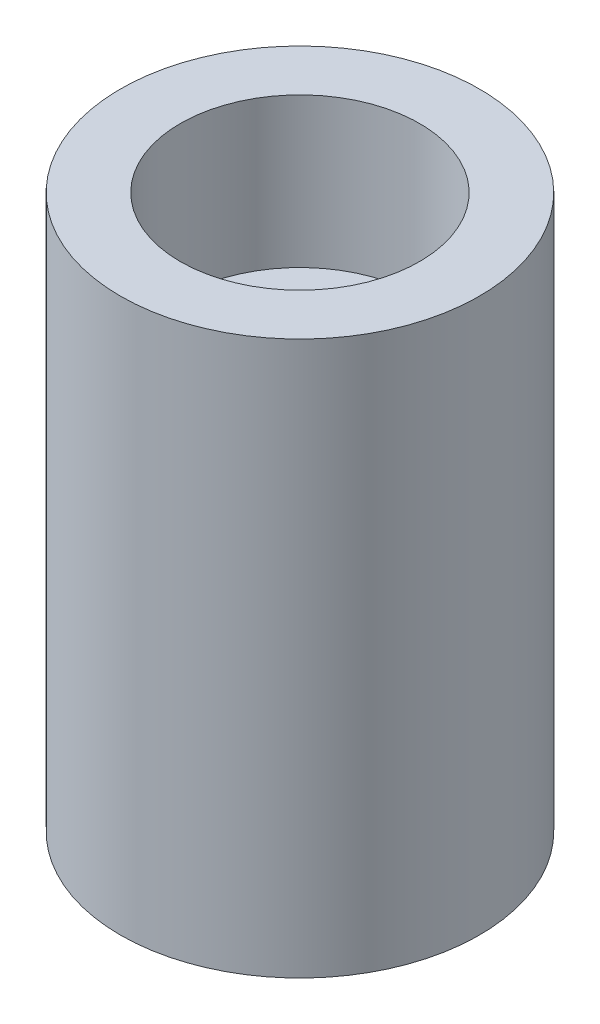
SolidWorks part; units mm, degrees
ref_plane "Front Plane" through (0, 0, 0) normal (0, 0, 1) x (1, 0, 0)
ref_plane "Top Plane" through (0, 0, 0) normal (0, 1, 0) x (1, 0, 0)
ref_plane "Right Plane" through (0, 0, 0) normal (1, 0, 0) x (0, 0, -1)
sketch "Sketch2" plane through (0, 0, 0) normal (0, 1, 0) x (1, 0, 0)
  circle A0 centre (0, 0) radius 6
  dimension "D1" = 12
extrude "Boss-Extrude2" add sketch "Sketch2" along normal blind 18.5
sketch "Sketch3" plane through (0, 18.5, 0) normal (0, 1, 0) x (1, 0, 0)
  circle A0 centre (0, 0) radius 4
  dimension "D1" = 8
extrude "Cut-Extrude1" cut sketch "Sketch3" against normal offset from surface (16.5 mm away) 2 up to face at (0, 0, 6)
sketch "Sketch4" plane through (0, 2, 0) normal (0, 1, 0) x (1, 0, 0)
  circle A0 centre (0, 0) radius 1.5
  dimension "D1" = 3
extrude "Cut-Extrude2" cut sketch "Sketch4" against normal up to next
sketch "Sketch5" plane through (0, 2, 0) normal (0, 1, 0) x (1, 0, 0)
  circle A0 centre (0, 0) radius 4
  circle A1 centre (0, 0) radius 3
  dimension "D1" = 6
extrude "Boss-Extrude3" add sketch "Sketch5" along normal offset from surface (11.5 mm away) 5 up to face at (0, 18.5, 4)
